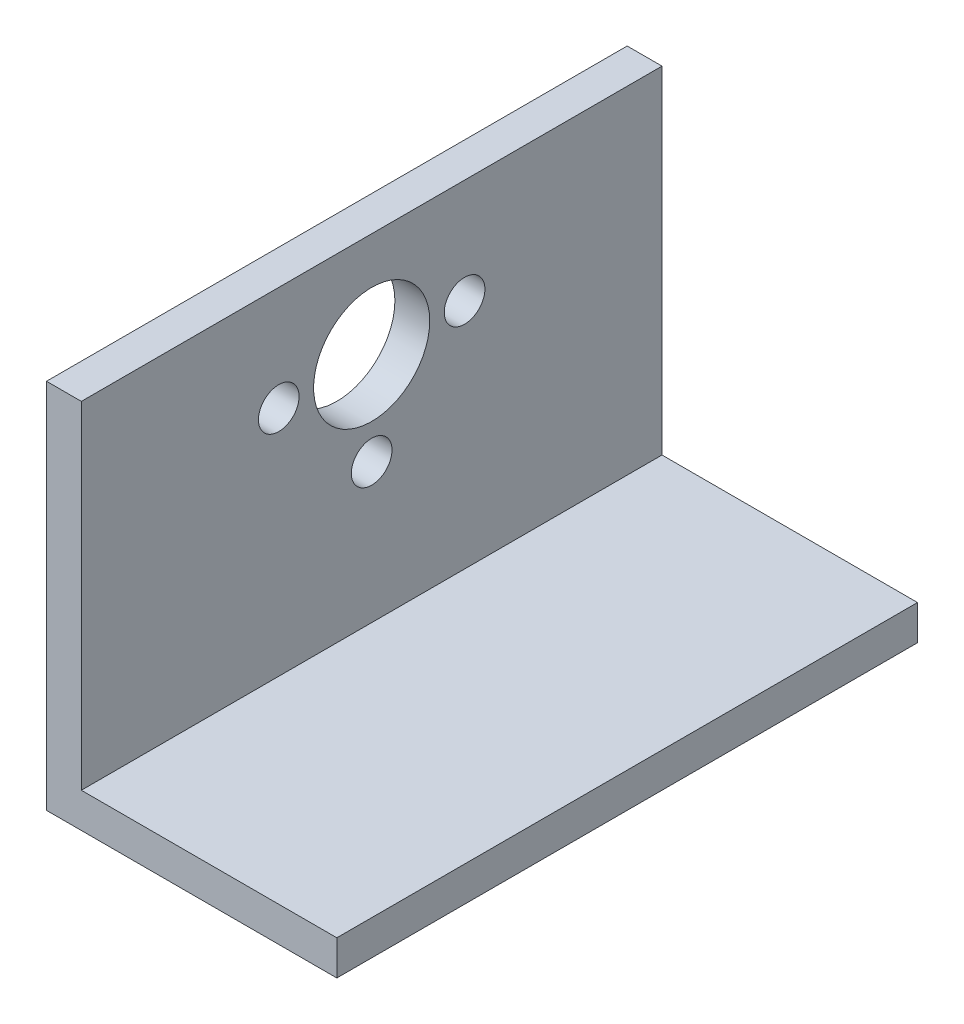
SolidWorks part; units mm, degrees
ref_plane "Front Plane" through (0, 0, 0) normal (0, 0, 1) x (1, 0, 0)
ref_plane "Top Plane" through (0, 0, 0) normal (0, 1, 0) x (1, 0, 0)
ref_plane "Right Plane" through (0, 0, 0) normal (1, 0, 0) x (0, 0, -1)
sketch "Sketch1" plane through (0, 0, 0) normal (0, 0, 1) x (1, 0, 0)
  line L0 (-7.8975, 31.3476) -> (-7.8975, 2.3476)
  line L1 (-7.8975, 2.3476) -> (14.1025, 2.3476)
  line L2 (14.1025, 2.3476) -> (14.1025, -0.6524)
  line L3 (14.1025, -0.6524) -> (-10.8975, -0.6524)
  line L4 (-10.8975, -0.6524) -> (-10.8975, 31.3476)
  line L5 (-10.8975, 31.3476) -> (-7.8975, 31.3476)
  dimension "D1" = 3
  dimension "D2" = 3
  dimension "D3" = 32
  dimension "D4" = 25
extrude "Boss-Extrude1" add sketch "Sketch1" along normal blind 50
hole_wizard "Hole for M5 300® SC Nuts (SP)1" positions "Sketch2" profile "Sketch3" hole size "M5x0.8" standard "PEM® Metric" end condition through all
sketch "Sketch2" plane through (-7.8975, 0, 0) normal (1, 0, 0) x (0, 0, -1)
  line L0 (-50, -0.6524) -> (0, -0.6524) construction
  line L1 (0, 2.3476) -> (0, 31.3476) construction
  point P0 (-25, 22.3476)
  dimension "D1" = 23
  dimension "D2" = 25
sketch "Sketch3" plane through (-7.8975, 22.3476, 25) normal (0, 1, 0) x (0, 0, -1)
  line L0 (0, 0) -> (0, 3)
  line L1 (0, 3) -> (5, 3)
  line L2 (5, 3) -> (5, 0)
  line L5 (5, 0) -> (0, 0)
  line L11 (0, -6.35) -> (0, 107.95) construction
  dimension "Thru Hole Dia." = 10
  dimension "Thru Hole Depth" = 3
hole_wizard "Hole for M5 300® SC Nuts (SP)2" positions "Sketch4" profile "Sketch5" hole size "M5x0.8" standard "PEM® Metric" end condition through all
sketch "Sketch4" plane through (-7.8975, 0, 0) normal (1, 0, 0) x (0, 0, -1)
  line L0 (-50, -0.6524) -> (0, -0.6524) construction
  line L1 (0, 2.3476) -> (0, 31.3476) construction
  circle A1 centre (-25, 22.3476) radius 5 construction
  point P0 (-17, 22.3476)
  point P2 (-33, 22.3476)
  point P4 (-25, 14.3476)
  dimension "D4" = 8
  dimension "D1" = 23
  dimension "D2" = 8
  dimension "D3" = 16
  dimension "D5" = 25
sketch "Sketch5" plane through (-7.8975, 22.3476, 17) normal (0, 1, 0) x (0, 0, -1)
  line L0 (0, 0) -> (0, 3)
  line L1 (0, 3) -> (1.75, 3)
  line L2 (1.75, 3) -> (1.75, 0)
  line L5 (1.75, 0) -> (0, 0)
  line L11 (0, -6.35) -> (0, 107.95) construction
  dimension "Thru Hole Dia." = 3.5
  dimension "Thru Hole Depth" = 3
